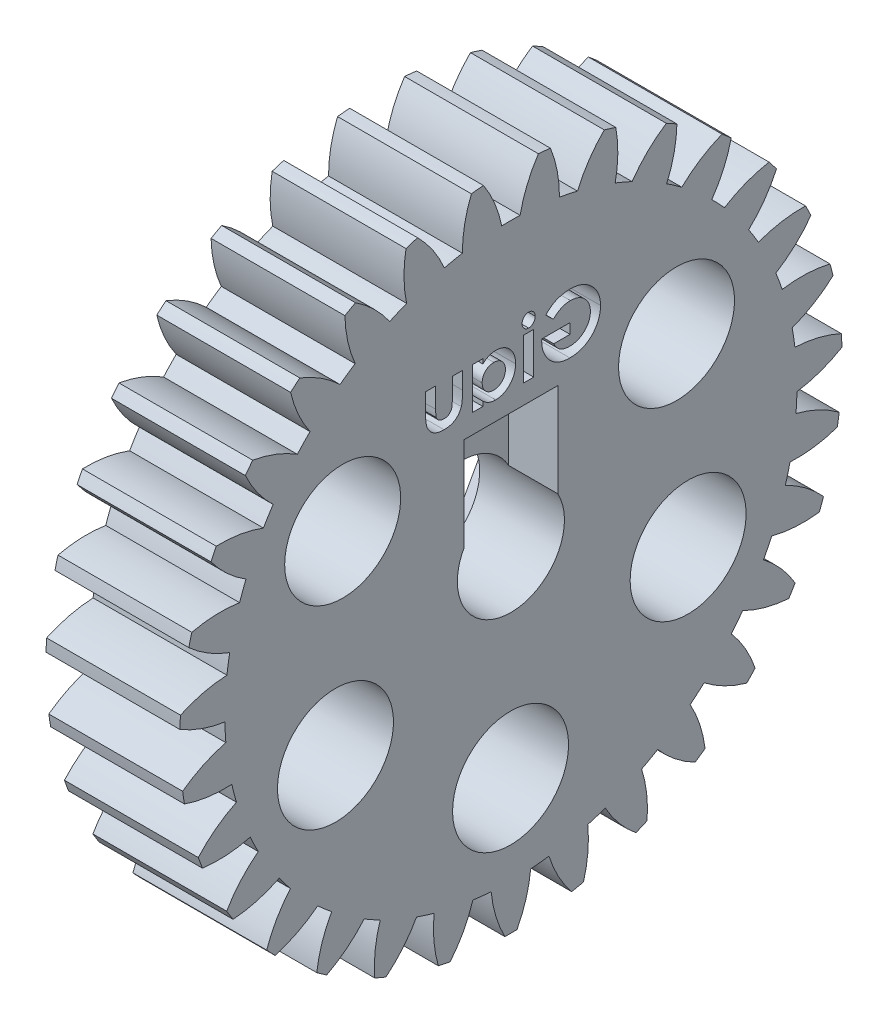
SolidWorks part; units mm, degrees
ref_plane "Plane1" through (0, 0, 0) normal (0, 0, 1) x (1, 0, 0)
ref_plane "Plane2" through (0, 0, 0) normal (0, 1, 0) x (1, 0, 0)
ref_plane "Plane3" through (0, 0, 0) normal (1, 0, 0) x (0, 0, -1)
sketch "HoldingSke" plane through (0, 0, 0) normal (0, 1, 0) x (1, 0, 0)
  line L0 (0, 0) -> (0.381, -0.2289)
  line L1 (-15, 0) -> (100, 0) construction
  line L2 (0, 0) -> (-2.1039, 2.3779)
  line L3 (0, 0) -> (-11.863, 4.5341)
  line L4 (0, 0) -> (7.4025, 4.4479)
  line L5 (0, 0) -> (-46.8476, -17.4728)
  line L6 (0, 0) -> (-12.4344, -8.3896)
  line L7 (-2.1039, 2.3779) -> (8.6586, 51.2059)
  line L8 (-76.2, 54.61) -> (-76.1, 54.61)
  line L9 (-71.009, 38.7566) -> (-53.1078, 45.2721)
  line L10 (-76.2, 71.12) -> (104.1128, 71.12)
  line L11 (0, 0) -> (-15, 0)
  line L12 (-76.2, 101.6) -> (-76.123, 101.6)
  line L13 (24.9733, 27.94) -> (52.9518, 28.4284)
  line L14 (24.9733, 27.94) -> (24.9743, 27.94)
  line L15 (24.9733, 27.94) -> (100.4006, 29.5858)
  line L16 (-63.627, -2.25) -> (-12.827, -2.25)
  circle A0 centre (0, 0) radius 0.4
  circle A1 centre (0, 0) radius 32.0615
  circle A2 centre (0, 0) radius 37.5
  circle A3 centre (0, 0) radius 0.4
  dimension "MHD" = 64.123
  dimension "Hub_dia" = 75
  dimension "Bore" = 0.8
  dimension "MBD" = 0.8
  dimension "Num_teeth" = 31
  dimension "Pitch_radius" = 180.3128
  dimension "Pitch" = 0.4444
  dimension "Width" = 15
  dimension "Overall_len" = 50
  dimension "Show_teeth" = 31
  dimension "Thickness" = 15
  dimension "OAL" = 50.0001
  dimension "T_dim" = 0.1
  dimension "Ap" = 20
  dimension "H" = 19.05
  dimension "Backlash" = 0.077
  dimension "Addendum_fac" = 1
  dimension "Dedendum_fac" = 1.25
  dimension "Clearance_fac" = 0.25
  dimension "Dedendum_add" = 0.001
  dimension "Module" = 2.25
sketch "BasProSke" plane through (0, 0, 0) normal (0, 1, 0) x (1, 0, 0)
  line L0 (-10, 0) -> (60, 0) construction
  line L1 (0, 0) -> (0, 37.125)
  line L2 (0, 0) -> (15, 0)
  line L3 (15, 0) -> (15, 37.125)
  line L4 (15, 37.125) -> (0, 37.125)
  dimension "Diameter" = 74.25
  dimension "Thickness" = 15
revolve "Base-Revolve" add sketch "BasProSke" angle 360 about L0
sketch "TooCutSke" plane through (0, 0, 0) normal (1, 0, 0) x (0, 0, -1)
  line L1 (0, 0) -> (0, 107) construction
  line L2 (0, 0) -> (-1.9011, 34.8231) construction
  line L3 (0, 0) -> (-7.0488, 69.3161) construction
  line L4 (-1.9011, 34.8231) -> (-3.5244, 34.6581) construction
  arc A0 (1.0309, 32.0449) -> (-1.0309, 32.0449) centre (0, 0) ccw
  arc A1 (3.0958, 37.0212) -> (-3.0958, 37.0212) centre (0, 0) ccw
  circle A2 centre (0, 0) radius 34.875 construction
  circle A3 centre (0, 0) radius 32.7718 construction
  arc A4 (-1.0309, 32.0449) -> (-3.0958, 37.0212) centre (-14.7056, 29.2871) ccw
  arc A5 (3.0958, 37.0212) -> (1.0309, 32.0449) centre (14.7056, 29.2871) ccw
  dimension "Root_dia" = 64.123
  dimension "Overcut_dia" = 74.3008
  dimension "Pitch_dia" = 69.75
  dimension "Base_dia" = 65.5436
  dimension "Flank_rad" = 13.95
  dimension "Half_ang" = 5.806
  dimension "Half_CT" = 1.6316
extrude "ToothCut" cut sketch "TooCutSke" along normal through all
fillet "Breaks" [suppressed] radius 0.045
fillet "RootFillets" [suppressed] radius 0.5635
pattern_circular "TeethCuts" count 31 over 360 about axis through (0, 0, 0) along (1, 0, 0) of "ToothCut", "RootFillets", "Breaks"
sketch "HubNeaOneSke" plane through (0, 0, 0) normal (-1, 0, 0) x (0, 0, 1)
  circle A0 centre (0, 0) radius 32.0615
  dimension "Diameter" = 64.123
extrude "HubNearOne" [suppressed] add sketch "HubNeaOneSke" along normal blind 35.0001
sketch "HubNeaBotSke" plane through (0, 0, 0) normal (-1, 0, 0) x (0, 0, 1)
  circle A0 centre (0, 0) radius 32.0615
  dimension "Diameter" = 64.123
extrude "HubNearBoth" [suppressed] add sketch "HubNeaBotSke" along normal blind 17.5
ref_plane "FarPln" through (15, 0, 0) normal (1, 0, 0) x (0, 0, -1)
sketch "HubFarSke" plane through (15, 0, 0) normal (1, 0, 0) x (0, 0, -1)
  circle A0 centre (0, 0) radius 32.0615
  dimension "Diameter" = 64.123
extrude "HubFar" [suppressed] add sketch "HubFarSke" along normal blind 17.5
sketch "BorSke" plane through (0, 0, 0) normal (1, 0, 0) x (0, 0, -1)
  circle A0 centre (0, 0) radius 6
  dimension "Diameter" = 12
extrude "Bore" cut sketch "BorSke" along normal mid plane 100.0001
sketch "KeySke" plane through (0, 0, 0) normal (1, 0, 0) x (0, 0, -1)
  line L0 (-0.05, 0) -> (-0.05, 0.5)
  line L1 (-0.05, 0.5) -> (0.05, 0.5)
  line L2 (0.05, 0.5) -> (0.05, 0)
  line L3 (0, 0) -> (0, 34) construction
  line L4 (-0.05, 0) -> (0.05, 0)
  dimension "Offset" = 0.5
  dimension "Width" = 0.1
extrude "Keyway" [suppressed] cut sketch "KeySke" along normal mid plane 100.0001
pattern_circular "Keyway2" [suppressed] count 2 every 90 about axis through (-10, 0, 0) along (1, 0, 0)
sketch "Sketch1" plane through (0, 0, 0) normal (-1, 0, 0) x (0, 0, 1)
  text T0 "<b>Giau</b>\r\n\r\n" font "Century Gothic" height 6.35
sketch "Sketch2" plane through (15, 0, 0) normal (1, 0, 0) x (0, 0, -1)
  line L2 (-5.25, 2.9047) -> (-5.25, 13.4047)
  line L3 (-5.25, 13.4047) -> (5.25, 13.4047)
  line L4 (5.25, 2.9047) -> (5.25, 13.4047)
  arc A0 (-5.25, 2.9047) -> (5.25, 2.9047) centre (0, 0) ccw
  circle A1 centre (0, 0) radius 6 construction
  dimension "D1" = 0
  dimension "D5" = 10.5
  dimension "D6" = 10.5
extrude "Cut-Extrude1" cut sketch "Sketch2" against normal blind 5.5
extrude "Cut-Extrude3" cut sketch "Sketch1" against normal through all
sketch "Sketch7" plane through (0, 0, 0) normal (-1, 0, 0) x (0, 0, 1)
sketch "Sketch8" plane through (0, 0, 0) normal (-1, 0, 0) x (0, 0, 1)
  line L1 (13.854, -0.2947) -> (7.1504, 11.8322)
  line L2 (7.1504, 11.8322) -> (-6.7036, 12.0901)
  line L3 (-6.7036, 12.0901) -> (-13.854, 0.2211)
  line L4 (-13.854, 0.2211) -> (-7.1504, -11.9057)
  line L5 (-7.1504, -11.9057) -> (6.7036, -12.1637)
  line L6 (6.7036, -12.1637) -> (13.854, -0.2947)
  circle A0 centre (0, -0.0368) radius 12 construction
  circle A1 centre (0, 0) radius 6 construction
  dimension "D1" = 0
  dimension "D2" = 24
extrude "Cut-Extrude5" cut sketch "Sketch8" against normal blind 5.5
sketch "Sketch10" plane through (0, 0, 0) normal (-1, 0, 0) x (0, 0, 1)
  line L0 (-6.7036, 12.0901) -> (-13.854, 0.2211) construction
  line L1 (13.854, -0.2947) -> (7.1504, 11.8322) construction
  line L2 (6.7036, -12.1637) -> (13.854, -0.2947) construction
  line L3 (-7.1504, -11.9057) -> (6.7036, -12.1637) construction
  line L4 (-13.854, 0.2211) -> (-7.1504, -11.9057) construction
  circle A0 centre (-19.8634, -9.5779) radius 6.5
  circle A1 centre (0.0405, -22.0413) radius 6.5
  circle A2 centre (19.6658, -10.0262) radius 6.5
  circle A3 centre (18.8582, 11.3227) radius 6.5
  circle A4 centre (-18.5625, 11.7841) radius 6.5
  dimension "D6" = 13
  dimension "D7" = 13
  dimension "D8" = 13
  dimension "D9" = 13
  dimension "D10" = 13
  dimension "D1" = 10
  dimension "D2" = 10
  dimension "D3" = 10
  dimension "D4" = 10
  dimension "D5" = 10
extrude "Cut-Extrude6" cut sketch "Sketch10" against normal through all
equation "' \"Module@HoldingSke\" = 6.35"
equation "' \"Num_teeth@HoldingSke\" = 12"
equation "' \"Ap@HoldingSke\" =  20"
equation "' \"Width@HoldingSke\" = 0.5 * 25.4"
equation "' \"Hub_dia@HoldingSke\"= 1 * 25.4"
equation "' \"Overall_len@HoldingSke\" = 1.0 * 25.4"
equation "' \"Bore@HoldingSke\" = 0.75 * 25.4"
equation "' \"T_dim@HoldingSke\" = 0.1 * 25.4"
equation "' \"Width@KeySke\" = 0.25 * 25.4"
equation "' \"Show_teeth@HoldingSke\" = 13"
equation "' \"Backlash@HoldingSke\" = 0.009 * 25.4"
equation "' \"Addendum_fac@HoldingSke\" = 1.0"
equation "' \"Dedendum_fac@HoldingSke\" = 1.25"
equation "' \"Dedendum_add@HoldingSke\" = 0.00005 * 25.4"
equation "' \"Clearance_fac@HoldingSke\" = 0.25"
equation "\"Pitch@HoldingSke\" = 1 / \"Module@HoldingSke\""
equation "\"Overcut_dia@TooCutSke\" = (\"Num_teeth@HoldingSke\" + 2 * \"Addendum_fac@HoldingSke\") / \"Pitch@HoldingSke\" + 0.002 * 25.4"
equation "\"Pitch_dia@TooCutSke\" = \"Num_teeth@HoldingSke\" / \"Pitch@HoldingSke\""
equation "\"Base_dia@TooCutSke\" = \"Num_teeth@HoldingSke\" / \"Pitch@HoldingSke\" * cos((\"Ap@HoldingSke\"  * 3.14159265 / 180))"
equation "\"Root_dia@TooCutSke\" = (\"Num_teeth@HoldingSke\" + 2) / \"Pitch@HoldingSke\" - 2 * (\"Addendum_fac@HoldingSke\" + \"Dedendum_fac@HoldingSke\") / \"Pitch@HoldingSke\" - \"Dedendum_add@HoldingSke\" * 2"
equation "\"Half_ang@TooCutSke\" = 180 / \"Num_teeth@HoldingSke\""
equation "\"Half_CT@TooCutSke\" = \"Num_teeth@HoldingSke\" / \"Pitch@HoldingSke\" * sin((3.14159265 / 2 / \"Num_teeth@HoldingSke\")) / 2 - 7 * \"Backlash@HoldingSke\" / 4"
equation "\"Flank_rad@TooCutSke\" = \"Num_teeth@HoldingSke\" / \"Pitch@HoldingSke\" / 5"
equation "\"Radius@RootFillets\" = \"Clearance_fac@HoldingSke\" / \"Pitch@HoldingSke\" + \"Dedendum_add@HoldingSke\""
equation "\"Break_rad@Breaks\" = 0.02 / \"Pitch@HoldingSke\""
equation "\"Thickness@HoldingSke\" = \"Width@HoldingSke\""
equation "\"OAL@HoldingSke\" = \"Thickness@HoldingSke\""
equation "\"MHD@HoldingSke\" = (\"Num_teeth@HoldingSke\" + 2) / \"Pitch@HoldingSke\" - 2 * (\"Addendum_fac@HoldingSke\" + \"Dedendum_fac@HoldingSke\")  / \"Pitch@HoldingSke\" - \"Dedendum_add@HoldingSke\" * 2"
equation "\"MBD@HoldingSke\" = (\"Num_teeth@HoldingSke\" + 2) / \"Pitch@HoldingSke\" - 2 * (\"Addendum_fac@HoldingSke\" + \"Dedendum_fac@HoldingSke\")  / \"Pitch@HoldingSke\" - \"Dedendum_add@HoldingSke\" * 2 - 0.002 * 25.4"
equation "\"MHD@HoldingSke\" = ((sgn( \"MHD@HoldingSke\" - \"Hub_dia@HoldingSke\" )-1)*( \"MHD@HoldingSke\" - \"Hub_dia@HoldingSke\" ))/-2+ \"Hub_dia@HoldingSke\""
equation "\"MBD@HoldingSke\" = ((sgn( \"MBD@HoldingSke\" - \"Bore@HoldingSke\" )-1)*( \"MBD@HoldingSke\" - \"Bore@HoldingSke\" ))/-2+ \"Bore@HoldingSke\""
equation "\"OAL@HoldingSke\" = ((sgn( \"OAL@HoldingSke\" - \"Overall_len@HoldingSke\" )+1)*( \"OAL@HoldingSke\" - \"Overall_len@HoldingSke\" ))/2 + \"Overall_len@HoldingSke\" + 0.000002 * 25.4"
equation "\"Num_teeth@TeethCuts\" = int( \"Show_teeth@HoldingSke\" ) + 1"
equation "\"Num_teeth@TeethCuts\" = ((sgn( \"Num_teeth@TeethCuts\" - \"Num_teeth@HoldingSke\" )-1)*( \"Num_teeth@TeethCuts\" - \"Num_teeth@HoldingSke\" ))/-2+ \"Num_teeth@HoldingSke\""
equation "\"Num_teeth@TeethCuts\" = ((sgn( \"Num_teeth@TeethCuts\" - 2.0)+1)*( \"Num_teeth@TeethCuts\" - 2.0))/2 +2.0"
equation "\"Angle@TeethCuts\" = 360.0 / \"Num_teeth@HoldingSke\""
equation "\"Diameter@BasProSke\" = (\"Num_teeth@HoldingSke\" + 2 * \"Addendum_fac@HoldingSke\") / \"Pitch@HoldingSke\""
equation "\"Thickness@BasProSke\"  = \"Thickness@HoldingSke\""
equation "' \"Fillet_rad@BasProSke\" =  \"Thickness@HoldingSke\" * 0.05"
equation "\"MHD@HoldingSke\" = ((sgn( \"MHD@HoldingSke\" - \"Root_dia@TooCutSke\" )-1)*( \"MHD@HoldingSke\" - \"Root_dia@TooCutSke\" ))/-2+ \"Root_dia@TooCutSke\""
equation "\"Diameter@HubNeaOneSke\" = \"MHD@HoldingSke\""
equation "\"Length@HubNearOne\" = \"OAL@HoldingSke\" - \"Thickness@BasProSke\""
equation "\"Diameter@HubNeaBotSke\" = \"MHD@HoldingSke\""
equation "\"Length@HubNearBoth\" = ( \"OAL@HoldingSke\" - \"Thickness@BasProSke\" ) / 2.0"
equation "\"Thickness@FarPln\" = \"Thickness@BasProSke\""
equation "\"Diameter@HubFarSke\" = \"MHD@HoldingSke\""
equation "\"Length@HubFar\" = ( \"OAL@HoldingSke\" - \"Thickness@BasProSke\" ) / 2.0"
equation "\"Diameter@BorSke\"=12"
equation "\"D1@Bore\" = \"OAL@HoldingSke\" * 2.0"
equation "\"D1@Keyway\" = \"OAL@HoldingSke\" * 2.0"
equation "\"Offset@KeySke\" = \"T_dim@HoldingSke\" + \"MBD@HoldingSke\" / 2.0"
